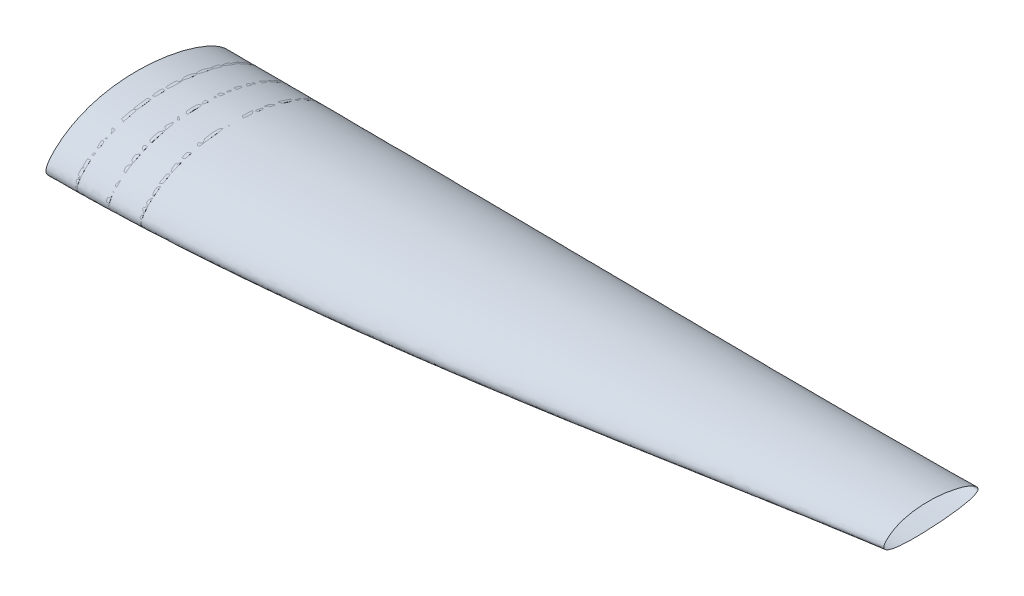
SolidWorks part; units mm, degrees
ref_plane "Ebene vorne" through (0, 0, 0) normal (0, 0, 1) x (1, 0, 0)
ref_plane "Ebene oben" through (0, 0, 0) normal (0, 1, 0) x (1, 0, 0)
ref_plane "Ebene rechts" through (0, 0, 0) normal (1, 0, 0) x (0, 0, -1)
sketch "Skizze1" plane through (0, 0, 0) normal (1, 0, 0) x (0, 0, -1)
  line L0 (0, 0) -> (-300, 0) construction
  spline S0 degree 3 poles (-6.4212, -30.087) (10.5374, 42.4945) (-200.2614, 100.4418) (-340.1049, -30.1519) (-153.9718, -21.531) (-6.4212, -30.087) (10.5374, 42.4945) (-200.2614, 100.4418) knots -0.489311 -0.255103 -0.02551 0 0.421873 0.510689 0.744897 0.97449 1 1.421873 1.510689 1.744897 only from (0, 0) to (0, 0)
  dimension "D1" = 300
ref_plane "Ebene1200" through (1200, 0, 0) normal (1, 0, 0) x (0, 0, -1)
sketch "Skizze2" plane through (1200, 0, 0) normal (1, 0, 0) x (0, 0, -1)
  line L0 (0, 0) -> (-150, 0) construction
  line L1 (0, 0) -> (-300, 0) construction
  spline S0 degree 3 poles (-68.4191, -18.4128) (55.8052, 1.825) (-102.4443, 41.9265) (-171.2197, -16.2346) (-68.4191, -18.4128) (55.8052, 1.825) (-102.4443, 41.9265) knots -0.555465 -0.497041 -0.235266 0 0.444535 0.502959 0.764734 1 1.444535 1.502959 1.764734 only from (0, 0) to (0, 0)
  dimension "D1" = 150
surface "Oberfläche-Ausformung1"
ref_plane "Ebene50-1" through (50, 0, 0) normal (1, 0, 0) x (0, 0, -1)
ref_plane "Ebene50-2" through (100, 0, 0) normal (1, 0, 0) x (0, 0, -1)
ref_plane "Ebene50-3" through (150, 0, 0) normal (1, 0, 0) x (0, 0, -1)
sketch "Skizze3" plane through (50, 0, 0) normal (1, 0, 0) x (0, 0, -1)
  spline S0 degree 3 poles (-26.456, 32.0396) (-29.8514, 34.0136) (-32.9269, 35.631) (-39.1645, 38.6583) (-42.3269, 40.0676) (-48.7229, 42.7159) (-51.9565, 43.9547) (-58.4854, 46.285) (-61.7806, 47.3765) (-66.7649, 48.9144) (-68.4327, 49.4102) (-71.7706, 50.367) (-73.4421, 50.8284) (-78.4639, 52.1641) (-81.8213, 52.99) (-91.9205, 55.2874) (-98.6889, 56.5802) (-112.2915, 58.7241) (-119.1258, 59.5749) (-132.8599, 60.8361) (-139.7597, 61.2464) (-150.1616, 61.5124) (-153.6415, 61.5424) (-160.5763, 61.4805) (-164.0357, 61.3889) (-174.3897, 60.9261) (-181.2597, 60.3679) (-194.9276, 58.6989) (-201.7255, 57.5888) (-211.8599, 55.4442) (-215.2276, 54.649) (-220.2618, 53.3244) (-221.937, 52.8609) (-225.2814, 51.8877) (-226.9503, 51.3779) (-235.2326, 48.7223) (-241.696, 46.2467) (-251.1125, 41.9308) (-254.2043, 40.3907) (-260.2844, 37.0864) (-263.2735, 35.324) (-267.6788, 32.5112) (-269.136, 31.544) (-272.0112, 29.5601) (-273.4299, 28.5432) (-276.2281, 26.4578) (-277.6076, 25.3893) (-280.3246, 23.197) (-281.6631, 22.0721) (-284.2873, 19.7645) (-285.5716, 18.5833) (-288.0755, 16.1573) (-289.2953, 14.9126) (-291.0651, 12.9866) (-291.645, 12.3347) (-292.7815, 11.008) (-293.3388, 10.3323) (-294.9643, 8.2712) (-295.9859, 6.8553) (-297.3765, 4.6359) (-297.8161, 3.88) (-298.6312, 2.3253) (-299.0027, 1.5343) (-299.6475, -0.0849) (-299.9205, -0.9133) (-300.2243, -2.1958) (-300.3075, -2.6295) (-300.4296, -3.4959) (-300.4689, -3.9303) (-300.4988, -4.8022) (-300.4893, -5.2395) (-300.4147, -6.1176) (-300.3495, -6.5545) (-300.0721, -7.8318) (-299.7775, -8.6495) (-299.1723, -9.8257) (-298.9457, -10.2044) (-298.4539, -10.9284) (-298.1878, -11.2755) (-297.6198, -11.9432) (-297.3164, -12.2651) (-296.6862, -12.8771) (-296.3596, -13.1675) (-295.3512, -13.9991) (-294.6409, -14.5013) (-293.1642, -15.4291) (-292.3942, -15.8561) (-290.0536, -17.0314) (-288.4498, -17.6809) (-285.1919, -18.8244) (-283.5371, -19.3162) (-280.193, -20.1933) (-278.5035, -20.578) (-275.0994, -21.2697) (-273.392, -21.575) (-269.9764, -22.1245) (-268.2669, -22.3689) (-263.1341, -23.0318) (-259.7069, -23.3815) (-252.8456, -23.9629) (-249.4115, -24.194) (-242.5385, -24.5748) (-239.0996, -24.7242) (-228.7779, -25.086) (-221.8901, -25.2136) (-208.1082, -25.3591) (-201.2135, -25.3757) (-187.4248, -25.3708) (-180.5304, -25.3485) (-166.7417, -25.3234) (-159.8474, -25.3214) (-139.1646, -25.421) (-125.3761, -25.6102) (-104.6944, -25.7676) (-97.8007, -25.7985) (-84.0149, -25.7415) (-77.1228, -25.6548) (-66.7869, -25.3462) (-63.342, -25.213) (-56.4532, -24.8616) (-53.0063, -24.6432) (-46.1322, -24.0858) (-42.7055, -23.7474) (-35.8831, -22.8932) (-32.4871, -22.3788) (-27.4297, -21.3967) (-25.7501, -21.0338) (-22.4073, -20.2136) (-20.7441, -19.7566) (-18.2664, -18.9725) (-17.4434, -18.6946) (-15.8044, -18.0985) (-14.99, -17.7808) (-12.5832, -16.7638) (-11.0199, -16.0004) (-8.77, -14.6591) (-8.0364, -14.1787) (-6.634, -13.1524) (-5.9624, -12.6048) (-4.6919, -11.4252) (-4.0917, -10.7923) (-2.9858, -9.4264) (-2.4937, -8.7087) (-1.6418, -7.1983) (-1.2803, -6.4056) (-0.6885, -4.7487) (-0.4655, -3.9065) (-0.1486, -2.1977) (-0.0543, -1.3311) (0.009, 0.4256) (-0.0233, 1.2965) (-0.2049, 3.0249) (-0.3543, 3.8823) (-0.6607, 5.1588) (-0.7767, 5.583) (-1.0319, 6.4176) (-1.1713, 6.8295) (-1.9228, 8.8638) (-2.6961, 10.412) (-4.0505, 12.6448) (-4.5359, 13.375) (-5.5488, 14.7873) (-6.078, 15.4724) (-7.7234, 17.4744) (-8.8971, 18.7382) (-11.3612, 21.158) (-12.6524, 22.3142) (-15.3271, 24.5375) (-16.7008, 25.5965) (-19.5063, 27.6299) (-20.9382, 28.6043) (-23.1227, 30.0127) (-23.857, 30.4734) (-24.9669, 31.152) (-25.3382, 31.3761) (-26.0837, 31.8204) (-26.456, 32.0396) (-29.8514, 34.0136) (-32.9269, 35.631) knots -0.001953 -0.001953 0 0 0.015625 0.015625 0.03125 0.03125 0.046875 0.046875 0.0625 0.0625 0.070313 0.070313 0.078125 0.078125 0.09375 0.09375 0.125 0.125 0.15625 0.15625 0.1875 0.1875 0.203125 0.203125 0.21875 0.21875 0.25 0.25 0.28125 0.28125 0.296875 0.296875 0.304688 0.304688 0.3125 0.3125 0.34375 0.34375 0.359375 0.359375 0.375 0.375 0.382813 0.382813 0.390625 0.390625 0.398438 0.398438 0.40625 0.40625 0.414063 0.414063 0.421875 0.421875 0.425781 0.425781 0.429688 0.429688 0.4375 0.4375 0.441406 0.441406 0.445313 0.445313 0.449219 0.449219 0.451172 0.451172 0.453125 0.453125 0.455078 0.455078 0.457031 0.457031 0.460938 0.460938 0.462891 0.462891 0.464844 0.464844 0.466797 0.466797 0.46875 0.46875 0.472656 0.472656 0.476563 0.476563 0.484375 0.484375 0.492188 0.492188 0.5 0.5 0.507813 0.507813 0.515625 0.515625 0.53125 0.53125 0.546875 0.546875 0.5625 0.5625 0.59375 0.59375 0.625 0.625 0.65625 0.65625 0.6875 0.6875 0.75 0.75 0.78125 0.78125 0.8125 0.8125 0.828125 0.828125 0.84375 0.84375 0.859375 0.859375 0.875 0.875 0.882813 0.882813 0.890625 0.890625 0.894531 0.894531 0.898438 0.898438 0.90625 0.90625 0.910156 0.910156 0.914063 0.914063 0.917969 0.917969 0.921875 0.921875 0.925781 0.925781 0.929688 0.929688 0.933594 0.933594 0.9375 0.9375 0.941406 0.941406 0.943359 0.943359 0.945313 0.945313 0.953125 0.953125 0.957031 0.957031 0.960938 0.960938 0.96875 0.96875 0.976563 0.976563 0.984375 0.984375 0.992188 0.992188 0.996094 0.996094 0.998047 0.998047 1 1 1.015625 1.015625 1.03125 only from (-26.8333, 32.2589) to (-26.8333, 32.2589)
  spline S1 degree 3 poles (-26.456, 32.0396) (-29.8514, 34.0136) (-32.9269, 35.631) (-39.1645, 38.6583) (-42.3269, 40.0676) (-48.7229, 42.7159) (-51.9565, 43.9547) (-58.4854, 46.285) (-61.7806, 47.3765) (-66.7649, 48.9144) (-68.4327, 49.4102) (-71.7706, 50.367) (-73.4421, 50.8284) (-78.4639, 52.1641) (-81.8213, 52.99) (-91.9205, 55.2874) (-98.6889, 56.5802) (-112.2915, 58.7241) (-119.1258, 59.5749) (-132.8599, 60.8361) (-139.7597, 61.2464) (-150.1616, 61.5124) (-153.6415, 61.5424) (-160.5763, 61.4805) (-164.0357, 61.3889) (-174.3897, 60.9261) (-181.2597, 60.3679) (-194.9276, 58.6989) (-201.7255, 57.5888) (-211.8599, 55.4442) (-215.2276, 54.649) (-220.2618, 53.3244) (-221.937, 52.8609) (-225.2814, 51.8877) (-226.9503, 51.3779) (-235.2326, 48.7223) (-241.696, 46.2467) (-251.1125, 41.9308) (-254.2043, 40.3907) (-260.2844, 37.0864) (-263.2735, 35.324) (-267.6788, 32.5112) (-269.136, 31.544) (-272.0112, 29.5601) (-273.4299, 28.5432) (-276.2281, 26.4578) (-277.6076, 25.3893) (-280.3246, 23.197) (-281.6631, 22.0721) (-284.2873, 19.7645) (-285.5716, 18.5833) (-288.0755, 16.1573) (-289.2953, 14.9126) (-291.0651, 12.9866) (-291.645, 12.3347) (-292.7815, 11.008) (-293.3388, 10.3323) (-294.9643, 8.2712) (-295.9859, 6.8553) (-297.3765, 4.6359) (-297.8161, 3.88) (-298.6312, 2.3253) (-299.0027, 1.5343) (-299.6475, -0.0849) (-299.9205, -0.9133) (-300.2243, -2.1958) (-300.3075, -2.6295) (-300.4296, -3.4959) (-300.4689, -3.9303) (-300.4988, -4.8022) (-300.4893, -5.2395) (-300.4147, -6.1176) (-300.3495, -6.5545) (-300.0721, -7.8318) (-299.7775, -8.6495) (-299.1723, -9.8257) (-298.9457, -10.2044) (-298.4539, -10.9284) (-298.1878, -11.2755) (-297.6198, -11.9432) (-297.3164, -12.2651) (-296.6862, -12.8771) (-296.3596, -13.1675) (-295.3512, -13.9991) (-294.6409, -14.5013) (-293.1642, -15.4291) (-292.3942, -15.8561) (-290.0536, -17.0314) (-288.4498, -17.6809) (-285.1919, -18.8244) (-283.5371, -19.3162) (-280.193, -20.1933) (-278.5035, -20.578) (-275.0994, -21.2697) (-273.392, -21.575) (-269.9764, -22.1245) (-268.2669, -22.3689) (-263.1341, -23.0318) (-259.7069, -23.3815) (-252.8456, -23.9629) (-249.4115, -24.194) (-242.5385, -24.5748) (-239.0996, -24.7242) (-228.7779, -25.086) (-221.8901, -25.2136) (-208.1082, -25.3591) (-201.2135, -25.3757) (-187.4248, -25.3708) (-180.5304, -25.3485) (-166.7417, -25.3234) (-159.8474, -25.3214) (-139.1646, -25.421) (-125.3761, -25.6102) (-104.6944, -25.7676) (-97.8007, -25.7985) (-84.0149, -25.7415) (-77.1228, -25.6548) (-66.7869, -25.3462) (-63.342, -25.213) (-56.4532, -24.8616) (-53.0063, -24.6432) (-46.1322, -24.0858) (-42.7055, -23.7474) (-35.8831, -22.8932) (-32.4871, -22.3788) (-27.4297, -21.3967) (-25.7501, -21.0338) (-22.4073, -20.2136) (-20.7441, -19.7566) (-18.2664, -18.9725) (-17.4434, -18.6946) (-15.8044, -18.0985) (-14.99, -17.7808) (-12.5832, -16.7638) (-11.0199, -16.0004) (-8.77, -14.6591) (-8.0364, -14.1787) (-6.634, -13.1524) (-5.9624, -12.6048) (-4.6919, -11.4252) (-4.0917, -10.7923) (-2.9858, -9.4264) (-2.4937, -8.7087) (-1.6418, -7.1983) (-1.2803, -6.4056) (-0.6885, -4.7487) (-0.4655, -3.9065) (-0.1486, -2.1977) (-0.0543, -1.3311) (0.009, 0.4256) (-0.0233, 1.2965) (-0.2049, 3.0249) (-0.3543, 3.8823) (-0.6607, 5.1588) (-0.7767, 5.583) (-1.0319, 6.4176) (-1.1713, 6.8295) (-1.9228, 8.8638) (-2.6961, 10.412) (-4.0505, 12.6448) (-4.5359, 13.375) (-5.5488, 14.7873) (-6.078, 15.4724) (-7.7234, 17.4744) (-8.8971, 18.7382) (-11.3612, 21.158) (-12.6524, 22.3142) (-15.3271, 24.5375) (-16.7008, 25.5965) (-19.5063, 27.6299) (-20.9382, 28.6043) (-23.1227, 30.0127) (-23.857, 30.4734) (-24.9669, 31.152) (-25.3382, 31.3761) (-26.0837, 31.8204) (-26.456, 32.0396) (-29.8514, 34.0136) (-32.9269, 35.631) knots -0.001953 -0.001953 0 0 0.015625 0.015625 0.03125 0.03125 0.046875 0.046875 0.0625 0.0625 0.070313 0.070313 0.078125 0.078125 0.09375 0.09375 0.125 0.125 0.15625 0.15625 0.1875 0.1875 0.203125 0.203125 0.21875 0.21875 0.25 0.25 0.28125 0.28125 0.296875 0.296875 0.304688 0.304688 0.3125 0.3125 0.34375 0.34375 0.359375 0.359375 0.375 0.375 0.382813 0.382813 0.390625 0.390625 0.398438 0.398438 0.40625 0.40625 0.414063 0.414063 0.421875 0.421875 0.425781 0.425781 0.429688 0.429688 0.4375 0.4375 0.441406 0.441406 0.445313 0.445313 0.449219 0.449219 0.451172 0.451172 0.453125 0.453125 0.455078 0.455078 0.457031 0.457031 0.460938 0.460938 0.462891 0.462891 0.464844 0.464844 0.466797 0.466797 0.46875 0.46875 0.472656 0.472656 0.476563 0.476563 0.484375 0.484375 0.492188 0.492188 0.5 0.5 0.507813 0.507813 0.515625 0.515625 0.53125 0.53125 0.546875 0.546875 0.5625 0.5625 0.59375 0.59375 0.625 0.625 0.65625 0.65625 0.6875 0.6875 0.75 0.75 0.78125 0.78125 0.8125 0.8125 0.828125 0.828125 0.84375 0.84375 0.859375 0.859375 0.875 0.875 0.882813 0.882813 0.890625 0.890625 0.894531 0.894531 0.898438 0.898438 0.90625 0.90625 0.910156 0.910156 0.914063 0.914063 0.917969 0.917969 0.921875 0.921875 0.925781 0.925781 0.929688 0.929688 0.933594 0.933594 0.9375 0.9375 0.941406 0.941406 0.943359 0.943359 0.945313 0.945313 0.953125 0.953125 0.957031 0.957031 0.960938 0.960938 0.96875 0.96875 0.976563 0.976563 0.984375 0.984375 0.992188 0.992188 0.996094 0.996094 0.998047 0.998047 1 1 1.015625 1.015625 1.03125 only from (-26.8333, 32.2589) to (-26.8333, 32.2589)
extrude "Aufsatz-Linear austragen1" add sketch "Skizze3" against normal blind 5
sketch "Skizze4" plane through (100, 0, 0) normal (1, 0, 0) x (0, 0, -1)
  spline S0 degree 3 poles (-25.3682, 31.2804) (-29.8789, 33.8946) (-32.9427, 35.5012) (-39.1561, 38.5087) (-42.3058, 39.9089) (-48.6758, 42.5402) (-51.896, 43.771) (-58.3974, 46.0865) (-61.6786, 47.171) (-66.6414, 48.6991) (-68.3023, 49.1918) (-71.6263, 50.1427) (-73.2908, 50.6013) (-78.2914, 51.9287) (-81.6346, 52.7494) (-91.6906, 55.0325) (-98.4296, 56.3172) (-111.9725, 58.4473) (-118.7764, 59.2923) (-132.4487, 60.5446) (-139.3172, 60.9518) (-149.6712, 61.2149) (-153.1358, 61.2443) (-160.0416, 61.1819) (-163.4866, 61.0903) (-173.7967, 60.6283) (-180.6372, 60.0719) (-194.2458, 58.4092) (-201.0138, 57.3036) (-211.1029, 55.1683) (-214.4553, 54.3766) (-219.4667, 53.058) (-221.1343, 52.5967) (-224.4634, 51.6279) (-226.1252, 51.1203) (-234.3724, 48.4761) (-240.808, 46.0114) (-250.1838, 41.7157) (-253.2623, 40.183) (-259.3159, 36.8946) (-262.2917, 35.1406) (-266.6773, 32.341) (-268.1279, 31.3783) (-270.9907, 29.4029) (-272.4031, 28.3903) (-275.1889, 26.3137) (-276.5622, 25.2497) (-279.2667, 23.0663) (-280.5991, 21.9458) (-283.2108, 19.6474) (-284.4888, 18.4708) (-286.9804, 16.054) (-288.1941, 14.8139) (-289.9547, 12.8947) (-290.5316, 12.2451) (-291.662, 10.923) (-292.2163, 10.2495) (-293.8319, 8.1962) (-294.8468, 6.7856) (-296.2276, 4.5743) (-296.664, 3.8212) (-297.4726, 2.2718) (-297.8412, 1.483) (-298.4797, -0.1312) (-298.7496, -0.957) (-299.0485, -2.2355) (-299.1299, -2.667) (-299.2485, -3.5294) (-299.2863, -3.9619) (-299.313, -4.8299) (-299.302, -5.2654) (-299.2245, -6.1398) (-299.158, -6.5738) (-298.8775, -7.8436) (-298.5815, -8.6566) (-297.9753, -9.8261) (-297.7488, -10.2021) (-297.2573, -10.9217) (-296.9916, -11.2666) (-296.4247, -11.9301) (-296.1221, -12.25) (-295.4938, -12.8582) (-295.1683, -13.1467) (-294.1634, -13.9732) (-293.4558, -14.4725) (-291.9851, -15.395) (-291.2184, -15.8197) (-288.8877, -16.9887) (-287.2911, -17.6351) (-284.0477, -18.773) (-282.4004, -19.2626) (-279.0716, -20.1359) (-277.3899, -20.519) (-274.0016, -21.2079) (-272.3015, -21.5121) (-268.9012, -22.0596) (-267.1993, -22.303) (-262.0895, -22.9636) (-258.6777, -23.3121) (-251.8472, -23.8916) (-248.4286, -24.1219) (-241.5866, -24.5013) (-238.1632, -24.6502) (-227.8881, -25.0105) (-221.0315, -25.1373) (-207.3119, -25.2811) (-200.4484, -25.2967) (-186.722, -25.2891) (-179.8587, -25.2652) (-166.1322, -25.2356) (-159.2689, -25.2305) (-138.6795, -25.3196) (-124.9531, -25.5012) (-104.3646, -25.6489) (-97.5021, -25.6768) (-83.7788, -25.6152) (-76.9179, -25.5269) (-66.6292, -25.2177) (-63.2001, -25.0847) (-56.343, -24.7344) (-52.9122, -24.5171) (-46.0661, -23.9628) (-42.654, -23.6266) (-35.8621, -22.7791) (-32.482, -22.2691) (-27.4503, -21.2968) (-25.7795, -20.9377) (-22.455, -20.1269) (-20.8013, -19.6754) (-18.3385, -18.9017) (-17.5206, -18.6276) (-15.892, -18.0402) (-15.0794, -17.7261) (-12.6695, -16.7168) (-11.1064, -15.9599) (-9.2348, -14.855) (-8.8647, -14.626) (-8.1338, -14.1498) (-7.7732, -13.9026) (-6.7176, -13.1381) (-6.0455, -12.5957) (-4.7772, -11.432) (-4.1809, -10.8109) (-3.3554, -9.8075) (-3.0918, -9.461) (-2.5909, -8.7409) (-2.3555, -8.3694) (-1.7055, -7.236) (-1.3418, -6.4494) (-0.8959, -5.225) (-0.7638, -4.8095) (-0.5327, -3.9638) (-0.4342, -3.5352) (-0.1903, -2.2494) (-0.0943, -1.3857) (-0.0433, -0.081) (-0.042, 0.3554) (-0.0708, 1.2312) (-0.1009, 1.6696) (-0.2354, 2.9714) (-0.384, 3.8274) (-0.687, 5.0951) (-0.8014, 5.515) (-1.0557, 6.3496) (-1.1961, 6.7654) (-1.9536, 8.8175) (-2.7298, 10.3636) (-4.0773, 12.5802) (-4.5575, 13.3017) (-5.5721, 14.7142) (-6.1078, 15.4064) (-7.7653, 17.4173) (-8.943, 18.6802) (-11.406, 21.0908) (-12.6918, 22.2381) (-15.3492, 24.4409) (-16.721, 25.4963) (-19.5354, 27.5308) (-20.9707, 28.5045) (-23.8879, 30.3798) (-25.3682, 31.2804) (-29.8789, 33.8946) (-32.9427, 35.5012) knots -0.007813 -0.007813 0 0 0.015625 0.015625 0.03125 0.03125 0.046875 0.046875 0.0625 0.0625 0.070312 0.070312 0.078125 0.078125 0.09375 0.09375 0.125 0.125 0.15625 0.15625 0.1875 0.1875 0.203125 0.203125 0.21875 0.21875 0.25 0.25 0.28125 0.28125 0.296875 0.296875 0.304687 0.304687 0.3125 0.3125 0.34375 0.34375 0.359375 0.359375 0.375 0.375 0.382812 0.382812 0.390625 0.390625 0.398437 0.398437 0.40625 0.40625 0.414062 0.414062 0.421875 0.421875 0.425781 0.425781 0.429687 0.429687 0.4375 0.4375 0.441406 0.441406 0.445312 0.445312 0.449219 0.449219 0.451172 0.451172 0.453125 0.453125 0.455078 0.455078 0.457031 0.457031 0.460937 0.460937 0.462891 0.462891 0.464844 0.464844 0.466797 0.466797 0.46875 0.46875 0.472656 0.472656 0.476562 0.476562 0.484375 0.484375 0.492187 0.492187 0.5 0.5 0.507812 0.507812 0.515625 0.515625 0.53125 0.53125 0.546875 0.546875 0.5625 0.5625 0.59375 0.59375 0.625 0.625 0.65625 0.65625 0.6875 0.6875 0.75 0.75 0.78125 0.78125 0.8125 0.8125 0.828125 0.828125 0.84375 0.84375 0.859375 0.859375 0.875 0.875 0.882812 0.882812 0.890625 0.890625 0.894531 0.894531 0.898437 0.898437 0.90625 0.90625 0.908203 0.908203 0.910156 0.910156 0.914062 0.914062 0.917969 0.917969 0.919922 0.919922 0.921875 0.921875 0.925781 0.925781 0.927734 0.927734 0.929687 0.929687 0.933594 0.933594 0.935547 0.935547 0.9375 0.9375 0.941406 0.941406 0.943359 0.943359 0.945312 0.945312 0.953125 0.953125 0.957031 0.957031 0.960937 0.960937 0.96875 0.96875 0.976562 0.976562 0.984375 0.984375 0.992187 0.992187 1 1 1.015625 1.015625 1.03125 only from (-26.8718, 32.1518) to (-26.8718, 32.1518)
  spline S1 degree 3 poles (-25.3682, 31.2804) (-29.8789, 33.8946) (-32.9427, 35.5012) (-39.1561, 38.5087) (-42.3058, 39.9089) (-48.6758, 42.5402) (-51.896, 43.771) (-58.3974, 46.0865) (-61.6786, 47.171) (-66.6414, 48.6991) (-68.3023, 49.1918) (-71.6263, 50.1427) (-73.2908, 50.6013) (-78.2914, 51.9287) (-81.6346, 52.7494) (-91.6906, 55.0325) (-98.4296, 56.3172) (-111.9725, 58.4473) (-118.7764, 59.2923) (-132.4487, 60.5446) (-139.3172, 60.9518) (-149.6712, 61.2149) (-153.1358, 61.2443) (-160.0416, 61.1819) (-163.4866, 61.0903) (-173.7967, 60.6283) (-180.6372, 60.0719) (-194.2458, 58.4092) (-201.0138, 57.3036) (-211.1029, 55.1683) (-214.4553, 54.3766) (-219.4667, 53.058) (-221.1343, 52.5967) (-224.4634, 51.6279) (-226.1252, 51.1203) (-234.3724, 48.4761) (-240.808, 46.0114) (-250.1838, 41.7157) (-253.2623, 40.183) (-259.3159, 36.8946) (-262.2917, 35.1406) (-266.6773, 32.341) (-268.1279, 31.3783) (-270.9907, 29.4029) (-272.4031, 28.3903) (-275.1889, 26.3137) (-276.5622, 25.2497) (-279.2667, 23.0663) (-280.5991, 21.9458) (-283.2108, 19.6474) (-284.4888, 18.4708) (-286.9804, 16.054) (-288.1941, 14.8139) (-289.9547, 12.8947) (-290.5316, 12.2451) (-291.662, 10.923) (-292.2163, 10.2495) (-293.8319, 8.1962) (-294.8468, 6.7856) (-296.2276, 4.5743) (-296.664, 3.8212) (-297.4726, 2.2718) (-297.8412, 1.483) (-298.4797, -0.1312) (-298.7496, -0.957) (-299.0485, -2.2355) (-299.1299, -2.667) (-299.2485, -3.5294) (-299.2863, -3.9619) (-299.313, -4.8299) (-299.302, -5.2654) (-299.2245, -6.1398) (-299.158, -6.5738) (-298.8775, -7.8436) (-298.5815, -8.6566) (-297.9753, -9.8261) (-297.7488, -10.2021) (-297.2573, -10.9217) (-296.9916, -11.2666) (-296.4247, -11.9301) (-296.1221, -12.25) (-295.4938, -12.8582) (-295.1683, -13.1467) (-294.1634, -13.9732) (-293.4558, -14.4725) (-291.9851, -15.395) (-291.2184, -15.8197) (-288.8877, -16.9887) (-287.2911, -17.6351) (-284.0477, -18.773) (-282.4004, -19.2626) (-279.0716, -20.1359) (-277.3899, -20.519) (-274.0016, -21.2079) (-272.3015, -21.5121) (-268.9012, -22.0596) (-267.1993, -22.303) (-262.0895, -22.9636) (-258.6777, -23.3121) (-251.8472, -23.8916) (-248.4286, -24.1219) (-241.5866, -24.5013) (-238.1632, -24.6502) (-227.8881, -25.0105) (-221.0315, -25.1373) (-207.3119, -25.2811) (-200.4484, -25.2967) (-186.722, -25.2891) (-179.8587, -25.2652) (-166.1322, -25.2356) (-159.2689, -25.2305) (-138.6795, -25.3196) (-124.9531, -25.5012) (-104.3646, -25.6489) (-97.5021, -25.6768) (-83.7788, -25.6152) (-76.9179, -25.5269) (-66.6292, -25.2177) (-63.2001, -25.0847) (-56.343, -24.7344) (-52.9122, -24.5171) (-46.0661, -23.9628) (-42.654, -23.6266) (-35.8621, -22.7791) (-32.482, -22.2691) (-27.4503, -21.2968) (-25.7795, -20.9377) (-22.455, -20.1269) (-20.8013, -19.6754) (-18.3385, -18.9017) (-17.5206, -18.6276) (-15.892, -18.0402) (-15.0794, -17.7261) (-12.6695, -16.7168) (-11.1064, -15.9599) (-9.2348, -14.855) (-8.8647, -14.626) (-8.1338, -14.1498) (-7.7732, -13.9026) (-6.7176, -13.1381) (-6.0455, -12.5957) (-4.7772, -11.432) (-4.1809, -10.8109) (-3.3554, -9.8075) (-3.0918, -9.461) (-2.5909, -8.7409) (-2.3555, -8.3694) (-1.7055, -7.236) (-1.3418, -6.4494) (-0.8959, -5.225) (-0.7638, -4.8095) (-0.5327, -3.9638) (-0.4342, -3.5352) (-0.1903, -2.2494) (-0.0943, -1.3857) (-0.0433, -0.081) (-0.042, 0.3554) (-0.0708, 1.2312) (-0.1009, 1.6696) (-0.2354, 2.9714) (-0.384, 3.8274) (-0.687, 5.0951) (-0.8014, 5.515) (-1.0557, 6.3496) (-1.1961, 6.7654) (-1.9536, 8.8175) (-2.7298, 10.3636) (-4.0773, 12.5802) (-4.5575, 13.3017) (-5.5721, 14.7142) (-6.1078, 15.4064) (-7.7653, 17.4173) (-8.943, 18.6802) (-11.406, 21.0908) (-12.6918, 22.2381) (-15.3492, 24.4409) (-16.721, 25.4963) (-19.5354, 27.5308) (-20.9707, 28.5045) (-23.8879, 30.3798) (-25.3682, 31.2804) (-29.8789, 33.8946) (-32.9427, 35.5012) knots -0.007813 -0.007813 0 0 0.015625 0.015625 0.03125 0.03125 0.046875 0.046875 0.0625 0.0625 0.070312 0.070312 0.078125 0.078125 0.09375 0.09375 0.125 0.125 0.15625 0.15625 0.1875 0.1875 0.203125 0.203125 0.21875 0.21875 0.25 0.25 0.28125 0.28125 0.296875 0.296875 0.304687 0.304687 0.3125 0.3125 0.34375 0.34375 0.359375 0.359375 0.375 0.375 0.382812 0.382812 0.390625 0.390625 0.398437 0.398437 0.40625 0.40625 0.414062 0.414062 0.421875 0.421875 0.425781 0.425781 0.429687 0.429687 0.4375 0.4375 0.441406 0.441406 0.445312 0.445312 0.449219 0.449219 0.451172 0.451172 0.453125 0.453125 0.455078 0.455078 0.457031 0.457031 0.460937 0.460937 0.462891 0.462891 0.464844 0.464844 0.466797 0.466797 0.46875 0.46875 0.472656 0.472656 0.476562 0.476562 0.484375 0.484375 0.492187 0.492187 0.5 0.5 0.507812 0.507812 0.515625 0.515625 0.53125 0.53125 0.546875 0.546875 0.5625 0.5625 0.59375 0.59375 0.625 0.625 0.65625 0.65625 0.6875 0.6875 0.75 0.75 0.78125 0.78125 0.8125 0.8125 0.828125 0.828125 0.84375 0.84375 0.859375 0.859375 0.875 0.875 0.882812 0.882812 0.890625 0.890625 0.894531 0.894531 0.898437 0.898437 0.90625 0.90625 0.908203 0.908203 0.910156 0.910156 0.914062 0.914062 0.917969 0.917969 0.919922 0.919922 0.921875 0.921875 0.925781 0.925781 0.927734 0.927734 0.929687 0.929687 0.933594 0.933594 0.935547 0.935547 0.9375 0.9375 0.941406 0.941406 0.943359 0.943359 0.945312 0.945312 0.953125 0.953125 0.957031 0.957031 0.960937 0.960937 0.96875 0.96875 0.976562 0.976562 0.984375 0.984375 0.992187 0.992187 1 1 1.015625 1.015625 1.03125 only from (-26.8718, 32.1518) to (-26.8718, 32.1518)
extrude "Aufsatz-Linear austragen2" add sketch "Skizze4" against normal blind 5 separate body
sketch "Skizze5" plane through (150, 0, 0) normal (1, 0, 0) x (0, 0, -1)
  spline S0 degree 3 poles (-26.561, 31.7616) (-29.9236, 33.7004) (-32.9681, 35.2894) (-39.1413, 38.2643) (-42.2702, 39.6495) (-48.5972, 42.2528) (-51.7954, 43.4707) (-58.2515, 45.7618) (-61.5096, 46.8349) (-66.4371, 48.3471) (-68.0865, 48.8348) (-71.3875, 49.776) (-73.0404, 50.2299) (-78.0061, 51.5438) (-81.3258, 52.3561) (-91.3106, 54.6159) (-98.0013, 55.8872) (-111.4457, 57.9948) (-118.1995, 58.8307) (-131.7702, 60.0688) (-138.587, 60.4708) (-147.1496, 60.6865) (-148.8642, 60.7152) (-152.2977, 60.7431) (-154.0155, 60.7423) (-159.1591, 60.6949) (-162.5802, 60.6034) (-172.8182, 60.1432) (-179.6104, 59.5899) (-193.1212, 57.9382) (-199.8401, 56.8405) (-209.8546, 54.721) (-213.1821, 53.9354) (-218.1558, 52.6269) (-219.8108, 52.1691) (-223.1147, 51.208) (-224.7647, 50.7041) (-232.9543, 48.0793) (-239.3446, 45.6332) (-248.6538, 41.3714) (-251.7104, 39.8511) (-257.7206, 36.5895) (-260.6749, 34.8497) (-265.0282, 32.0723) (-266.468, 31.1171) (-269.3104, 29.1562) (-270.7127, 28.1509) (-273.4781, 26.0891) (-274.8414, 25.0325) (-277.5257, 22.8641) (-278.848, 21.7513) (-281.4395, 19.4684) (-282.7075, 18.2995) (-285.1792, 15.8983) (-286.383, 14.666) (-288.1289, 12.7586) (-288.7009, 12.1129) (-289.8216, 10.7986) (-290.3711, 10.1291) (-291.971, 8.0891) (-292.9757, 6.6875) (-294.3413, 4.4902) (-294.7727, 3.7417) (-295.5716, 2.2019) (-295.9359, 1.4168) (-296.5656, -0.1884) (-296.8312, -1.0095) (-297.1237, -2.2807) (-297.2027, -2.7086) (-297.3172, -3.5645) (-297.3529, -3.9938) (-297.376, -4.8555) (-297.3633, -5.2879) (-297.2827, -6.1561) (-297.215, -6.5858) (-296.9317, -7.8445) (-296.635, -8.6502) (-296.0297, -9.8092) (-295.8038, -10.1818) (-295.3142, -10.8948) (-295.0496, -11.2366) (-294.4857, -11.8941) (-294.1847, -12.2112) (-293.5602, -12.8141) (-293.2368, -13.1001) (-292.2384, -13.9196) (-291.5357, -14.4147) (-290.0757, -15.3297) (-289.3147, -15.7509) (-287.0005, -16.9115) (-285.4155, -17.5533) (-282.1962, -18.6836) (-280.5614, -19.17) (-277.2579, -20.0378) (-275.5891, -20.4185) (-272.227, -21.1033) (-270.5386, -21.406) (-267.1629, -21.9507) (-265.4734, -22.1929) (-260.4008, -22.8502) (-257.0139, -23.197) (-250.2335, -23.7738) (-246.84, -24.003) (-240.0483, -24.3806) (-236.6502, -24.5287) (-226.4509, -24.887) (-219.6449, -25.0126) (-206.0268, -25.1537) (-199.2142, -25.1678) (-178.7763, -25.1501) (-165.1509, -25.0587) (-137.9006, -25.1544) (-124.2753, -25.3237) (-103.8387, -25.4556) (-97.0268, -25.4788) (-83.4052, -25.4098) (-76.5954, -25.3189) (-66.3838, -25.0088) (-62.9805, -24.8761) (-56.1753, -24.5279) (-52.7735, -24.3127) (-45.9719, -23.7637) (-42.5801, -23.4309) (-35.8363, -22.5942) (-32.4824, -22.0915) (-27.4946, -21.1359) (-25.8393, -20.7834) (-22.5477, -19.989) (-20.9114, -19.5472) (-17.6651, -18.5407) (-16.055, -17.9766) (-13.6688, -16.9944) (-12.8783, -16.6441) (-11.3097, -15.8852) (-10.5366, -15.4787) (-9.0327, -14.6072) (-8.2998, -14.1414) (-7.236, -13.3862) (-6.8874, -13.125) (-6.2038, -12.5812) (-5.869, -12.2987) (-4.9002, -11.4264) (-4.2971, -10.8086) (-3.1905, -9.4889) (-2.6871, -8.7868) (-2.0232, -7.6566) (-1.8166, -7.2661) (-1.4431, -6.4777) (-1.2747, -6.0777) (-0.8223, -4.8612) (-0.5905, -4.0283) (-0.2571, -2.3217) (-0.156, -1.4438) (-0.0834, 0.2959) (-0.1109, 1.1643) (-0.2871, 2.8982) (-0.4374, 3.7673) (-0.842, 5.4579) (-1.0964, 6.2849) (-1.6961, 7.9067) (-2.0413, 8.7017) (-2.6193, 9.8729) (-2.8226, 10.2607) (-3.2451, 11.0243) (-3.4642, 11.4) (-4.5955, 13.2508) (-5.6137, 14.6437) (-7.8147, 17.3018) (-8.9995, 18.568) (-11.4923, 20.9942) (-12.787, 22.1415) (-15.4503, 24.3353) (-16.8191, 25.3815) (-19.6168, 27.392) (-21.0457, 28.3563) (-23.2269, 29.7511) (-23.9603, 30.2074) (-25.0692, 30.8798) (-25.4403, 31.1019) (-26.1854, 31.5423) (-26.561, 31.7616) (-29.9236, 33.7004) (-32.9681, 35.2894) knots -0.001953 -0.001953 0 0 0.015625 0.015625 0.03125 0.03125 0.046875 0.046875 0.0625 0.0625 0.070313 0.070313 0.078125 0.078125 0.09375 0.09375 0.125 0.125 0.15625 0.15625 0.1875 0.1875 0.195313 0.195313 0.203125 0.203125 0.21875 0.21875 0.25 0.25 0.28125 0.28125 0.296875 0.296875 0.304688 0.304688 0.3125 0.3125 0.34375 0.34375 0.359375 0.359375 0.375 0.375 0.382813 0.382813 0.390625 0.390625 0.398438 0.398438 0.40625 0.40625 0.414063 0.414063 0.421875 0.421875 0.425781 0.425781 0.429688 0.429688 0.4375 0.4375 0.441406 0.441406 0.445313 0.445313 0.449219 0.449219 0.451172 0.451172 0.453125 0.453125 0.455078 0.455078 0.457031 0.457031 0.460938 0.460938 0.462891 0.462891 0.464844 0.464844 0.466797 0.466797 0.46875 0.46875 0.472656 0.472656 0.476563 0.476563 0.484375 0.484375 0.492188 0.492188 0.5 0.5 0.507813 0.507813 0.515625 0.515625 0.53125 0.53125 0.546875 0.546875 0.5625 0.5625 0.59375 0.59375 0.625 0.625 0.6875 0.6875 0.75 0.75 0.78125 0.78125 0.8125 0.8125 0.828125 0.828125 0.84375 0.84375 0.859375 0.859375 0.875 0.875 0.882813 0.882813 0.890625 0.890625 0.898438 0.898438 0.902344 0.902344 0.90625 0.90625 0.910156 0.910156 0.912109 0.912109 0.914063 0.914063 0.917969 0.917969 0.921875 0.921875 0.923828 0.923828 0.925781 0.925781 0.929688 0.929688 0.933594 0.933594 0.9375 0.9375 0.941406 0.941406 0.945313 0.945313 0.949219 0.949219 0.951172 0.951172 0.953125 0.953125 0.960938 0.960938 0.96875 0.96875 0.976563 0.976563 0.984375 0.984375 0.992188 0.992188 0.996094 0.996094 0.998047 0.998047 1 1 1.015625 1.015625 1.03125 only from (-26.9346, 31.977) to (-26.9346, 31.977)
  spline S1 degree 3 poles (-26.561, 31.7616) (-29.9236, 33.7004) (-32.9681, 35.2894) (-39.1413, 38.2643) (-42.2702, 39.6495) (-48.5972, 42.2528) (-51.7954, 43.4707) (-58.2515, 45.7618) (-61.5096, 46.8349) (-66.4371, 48.3471) (-68.0865, 48.8348) (-71.3875, 49.776) (-73.0404, 50.2299) (-78.0061, 51.5438) (-81.3258, 52.3561) (-91.3106, 54.6159) (-98.0013, 55.8872) (-111.4457, 57.9948) (-118.1995, 58.8307) (-131.7702, 60.0688) (-138.587, 60.4708) (-147.1496, 60.6865) (-148.8642, 60.7152) (-152.2977, 60.7431) (-154.0155, 60.7423) (-159.1591, 60.6949) (-162.5802, 60.6034) (-172.8182, 60.1432) (-179.6104, 59.5899) (-193.1212, 57.9382) (-199.8401, 56.8405) (-209.8546, 54.721) (-213.1821, 53.9354) (-218.1558, 52.6269) (-219.8108, 52.1691) (-223.1147, 51.208) (-224.7647, 50.7041) (-232.9543, 48.0793) (-239.3446, 45.6332) (-248.6538, 41.3714) (-251.7104, 39.8511) (-257.7206, 36.5895) (-260.6749, 34.8497) (-265.0282, 32.0723) (-266.468, 31.1171) (-269.3104, 29.1562) (-270.7127, 28.1509) (-273.4781, 26.0891) (-274.8414, 25.0325) (-277.5257, 22.8641) (-278.848, 21.7513) (-281.4395, 19.4684) (-282.7075, 18.2995) (-285.1792, 15.8983) (-286.383, 14.666) (-288.1289, 12.7586) (-288.7009, 12.1129) (-289.8216, 10.7986) (-290.3711, 10.1291) (-291.971, 8.0891) (-292.9757, 6.6875) (-294.3413, 4.4902) (-294.7727, 3.7417) (-295.5716, 2.2019) (-295.9359, 1.4168) (-296.5656, -0.1884) (-296.8312, -1.0095) (-297.1237, -2.2807) (-297.2027, -2.7086) (-297.3172, -3.5645) (-297.3529, -3.9938) (-297.376, -4.8555) (-297.3633, -5.2879) (-297.2827, -6.1561) (-297.215, -6.5858) (-296.9317, -7.8445) (-296.635, -8.6502) (-296.0297, -9.8092) (-295.8038, -10.1818) (-295.3142, -10.8948) (-295.0496, -11.2366) (-294.4857, -11.8941) (-294.1847, -12.2112) (-293.5602, -12.8141) (-293.2368, -13.1001) (-292.2384, -13.9196) (-291.5357, -14.4147) (-290.0757, -15.3297) (-289.3147, -15.7509) (-287.0005, -16.9115) (-285.4155, -17.5533) (-282.1962, -18.6836) (-280.5614, -19.17) (-277.2579, -20.0378) (-275.5891, -20.4185) (-272.227, -21.1033) (-270.5386, -21.406) (-267.1629, -21.9507) (-265.4734, -22.1929) (-260.4008, -22.8502) (-257.0139, -23.197) (-250.2335, -23.7738) (-246.84, -24.003) (-240.0483, -24.3806) (-236.6502, -24.5287) (-226.4509, -24.887) (-219.6449, -25.0126) (-206.0268, -25.1537) (-199.2142, -25.1678) (-178.7763, -25.1501) (-165.1509, -25.0587) (-137.9006, -25.1544) (-124.2753, -25.3237) (-103.8387, -25.4556) (-97.0268, -25.4788) (-83.4052, -25.4098) (-76.5954, -25.3189) (-66.3838, -25.0088) (-62.9805, -24.8761) (-56.1753, -24.5279) (-52.7735, -24.3127) (-45.9719, -23.7637) (-42.5801, -23.4309) (-35.8363, -22.5942) (-32.4824, -22.0915) (-27.4946, -21.1359) (-25.8393, -20.7834) (-22.5477, -19.989) (-20.9114, -19.5472) (-17.6651, -18.5407) (-16.055, -17.9766) (-13.6688, -16.9944) (-12.8783, -16.6441) (-11.3097, -15.8852) (-10.5366, -15.4787) (-9.0327, -14.6072) (-8.2998, -14.1414) (-7.236, -13.3862) (-6.8874, -13.125) (-6.2038, -12.5812) (-5.869, -12.2987) (-4.9002, -11.4264) (-4.2971, -10.8086) (-3.1905, -9.4889) (-2.6871, -8.7868) (-2.0232, -7.6566) (-1.8166, -7.2661) (-1.4431, -6.4777) (-1.2747, -6.0777) (-0.8223, -4.8612) (-0.5905, -4.0283) (-0.2571, -2.3217) (-0.156, -1.4438) (-0.0834, 0.2959) (-0.1109, 1.1643) (-0.2871, 2.8982) (-0.4374, 3.7673) (-0.842, 5.4579) (-1.0964, 6.2849) (-1.6961, 7.9067) (-2.0413, 8.7017) (-2.6193, 9.8729) (-2.8226, 10.2607) (-3.2451, 11.0243) (-3.4642, 11.4) (-4.5955, 13.2508) (-5.6137, 14.6437) (-7.8147, 17.3018) (-8.9995, 18.568) (-11.4923, 20.9942) (-12.787, 22.1415) (-15.4503, 24.3353) (-16.8191, 25.3815) (-19.6168, 27.392) (-21.0457, 28.3563) (-23.2269, 29.7511) (-23.9603, 30.2074) (-25.0692, 30.8798) (-25.4403, 31.1019) (-26.1854, 31.5423) (-26.561, 31.7616) (-29.9236, 33.7004) (-32.9681, 35.2894) knots -0.001953 -0.001953 0 0 0.015625 0.015625 0.03125 0.03125 0.046875 0.046875 0.0625 0.0625 0.070313 0.070313 0.078125 0.078125 0.09375 0.09375 0.125 0.125 0.15625 0.15625 0.1875 0.1875 0.195313 0.195313 0.203125 0.203125 0.21875 0.21875 0.25 0.25 0.28125 0.28125 0.296875 0.296875 0.304688 0.304688 0.3125 0.3125 0.34375 0.34375 0.359375 0.359375 0.375 0.375 0.382813 0.382813 0.390625 0.390625 0.398438 0.398438 0.40625 0.40625 0.414063 0.414063 0.421875 0.421875 0.425781 0.425781 0.429688 0.429688 0.4375 0.4375 0.441406 0.441406 0.445313 0.445313 0.449219 0.449219 0.451172 0.451172 0.453125 0.453125 0.455078 0.455078 0.457031 0.457031 0.460938 0.460938 0.462891 0.462891 0.464844 0.464844 0.466797 0.466797 0.46875 0.46875 0.472656 0.472656 0.476563 0.476563 0.484375 0.484375 0.492188 0.492188 0.5 0.5 0.507813 0.507813 0.515625 0.515625 0.53125 0.53125 0.546875 0.546875 0.5625 0.5625 0.59375 0.59375 0.625 0.625 0.6875 0.6875 0.75 0.75 0.78125 0.78125 0.8125 0.8125 0.828125 0.828125 0.84375 0.84375 0.859375 0.859375 0.875 0.875 0.882813 0.882813 0.890625 0.890625 0.898438 0.898438 0.902344 0.902344 0.90625 0.90625 0.910156 0.910156 0.912109 0.912109 0.914063 0.914063 0.917969 0.917969 0.921875 0.921875 0.923828 0.923828 0.925781 0.925781 0.929688 0.929688 0.933594 0.933594 0.9375 0.9375 0.941406 0.941406 0.945313 0.945313 0.949219 0.949219 0.951172 0.951172 0.953125 0.953125 0.960938 0.960938 0.96875 0.96875 0.976563 0.976563 0.984375 0.984375 0.992188 0.992188 0.996094 0.996094 0.998047 0.998047 1 1 1.015625 1.015625 1.03125 only from (-26.9346, 31.977) to (-26.9346, 31.977)
extrude "Aufsatz-Linear austragen3" add sketch "Skizze5" against normal blind 5 separate body
sketch "Skizze6" plane through (0, 0, 0) normal (1, 0, 0) x (0, 0, -1)
  line L1 (-43.0514, -10.1983) -> (-99.8294, -10.1983)
  line L2 (-43.0514, -10.1983) -> (-43.0514, -33.2899)
  line L3 (-43.0514, -33.2899) -> (-99.8294, -33.2899)
  line L4 (-99.8294, -10.1983) -> (-99.8294, -33.2899)
extrude "Schnitt-Linear austragen2" cut sketch "Skizze6" along normal through all
